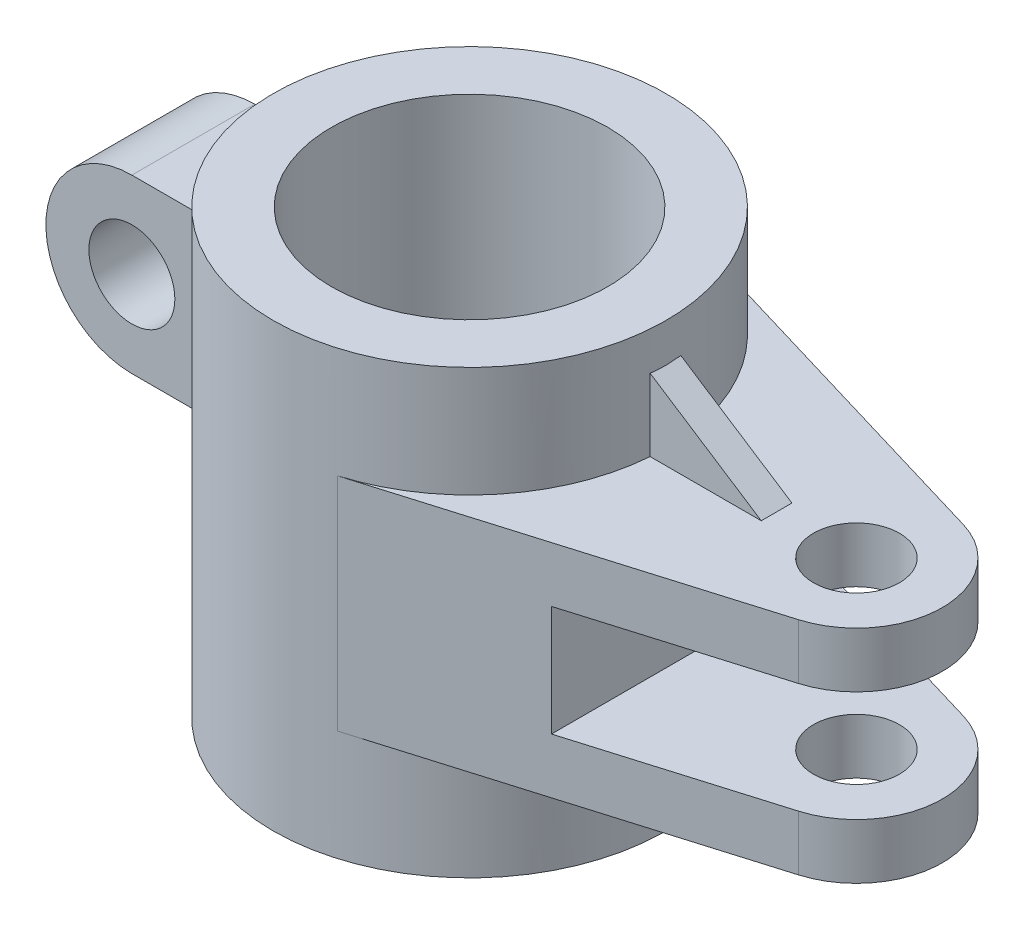
SolidWorks part; units mm, degrees
ref_plane "前视基准面" through (0, 0, 0) normal (0, 0, 1) x (1, 0, 0)
ref_plane "上视基准面" through (0, 0, 0) normal (0, 1, 0) x (1, 0, 0)
ref_plane "右视基准面" through (0, 0, 0) normal (1, 0, 0) x (0, 0, -1)
sketch "草图1" plane through (0, 0, 0) normal (0, 1, 0) x (1, 0, 0)
  circle A0 centre (0, 0) radius 22.5
  circle A1 centre (0, 0) radius 32
extrude "凸台-拉伸1" add sketch "草图1" along normal blind 72
ref_plane "基准面1" through (0, 54, 0) normal (0, 1, 0) x (1, 0, 0)
ref_plane "基准面2" through (0, 18, 0) normal (0, 1, 0) x (1, 0, 0)
ref_plane "基准面3" through (0, 36, 0) normal (0, 1, 0) x (1, 0, 0)
sketch "草图2" plane through (0, 18, 0) normal (0, 1, 0) x (1, 0, 0)
  line L1 (9.1429, 30.6661) -> (67, 13.4164)
  line L2 (9.1429, -30.6661) -> (67, -13.4164)
  circle A0 centre (63, 0) radius 7
  arc A1 (67, -13.4164) -> (67, 13.4164) centre (63, 0) ccw
  circle A2 centre (0, 0) radius 32 construction
  arc A3 (9.1429, 30.6661) -> (9.1429, -30.6661) centre (0, 0) cw
extrude "凸台-拉伸2" add sketch "草图2" along normal blind 36
sketch "草图3" plane through (0, 36, 0) normal (0, 1, 0) x (1, 0, 0)
  line L1 (36, 22.6588) -> (36, -22.6588)
  line L2 (67, 13.4164) -> (9.1429, 30.6661) construction
  line L3 (9.1429, -30.6661) -> (67, -13.4164) construction
  line L4 (36, -22.6588) -> (67, -13.4164)
  line L5 (36, 22.6588) -> (67, 13.4164)
  arc A0 (67, -13.4164) -> (67, 13.4164) centre (63, 0) ccw construction
  arc A1 (67, -13.4164) -> (67, 13.4164) centre (63, 0) ccw
extrude "切除-拉伸1" cut sketch "草图3" against normal mid plane 18
ref_plane "基准面4" through (0, 45, 0) normal (0, 1, 0) x (1, 0, 0)
sketch "草图4" plane through (0, 45, 0) normal (0, 1, 0) x (1, 0, 0)
  line L1 (-30.3305, 10) -> (-45, 10)
  line L2 (-45, 10) -> (-59, 10)
  line L3 (-59, 10) -> (-59, -10)
  line L5 (-45, -10) -> (-59, -10)
  line L6 (-30.3305, -10) -> (-45, -10)
  arc A0 (-30.3305, 10) -> (-30.3305, -10) centre (0, 0) ccw
extrude "凸台-拉伸3" add sketch "草图4" along normal mid plane 28
sketch "草图5" plane through (0, 0, 0) normal (0, 0, 1) x (1, 0, 0)
  line L2 (35.2, 45) -> (-35.2, 45) construction
  circle A1 centre (-45, 45) radius 7
extrude "切除-拉伸2" cut sketch "草图5" against normal through all both and the other way through all
sketch "草图6" plane through (0, 0, 10) normal (0, 0, 1) x (1, 0, 0)
  line L0 (35.2, 45) -> (-35.2, 45) construction
  line L1 (-45, 59) -> (-45, 73.3905)
  line L2 (-45, 73.3905) -> (-74.1617, 70.1672)
  line L3 (-74.1617, 70.1672) -> (-67.7151, 21.1727)
  line L6 (-67.7151, 21.1727) -> (-45.4248, 31.0064)
  arc A2 (-45, 59) -> (-45.4248, 31.0064) centre (-45, 45) ccw
extrude "切除-拉伸3" cut sketch "草图6" against normal through all both and the other way through all contours L2 L3 L6 A2 L1
sketch "草图7" plane through (0, 0, 0) normal (0, 0, 1) x (1, 0, 0)
  line L2 (35.2, 54) -> (-35.2, 54) construction
  line L3 (50, 54) -> (28.9873, 67.6458)
  line L4 (28.9873, 67.6458) -> (28.9873, 54)
  line L5 (28.9873, 54) -> (50, 54)
extrude "凸台-拉伸4" add sketch "草图7" along normal mid plane 5
